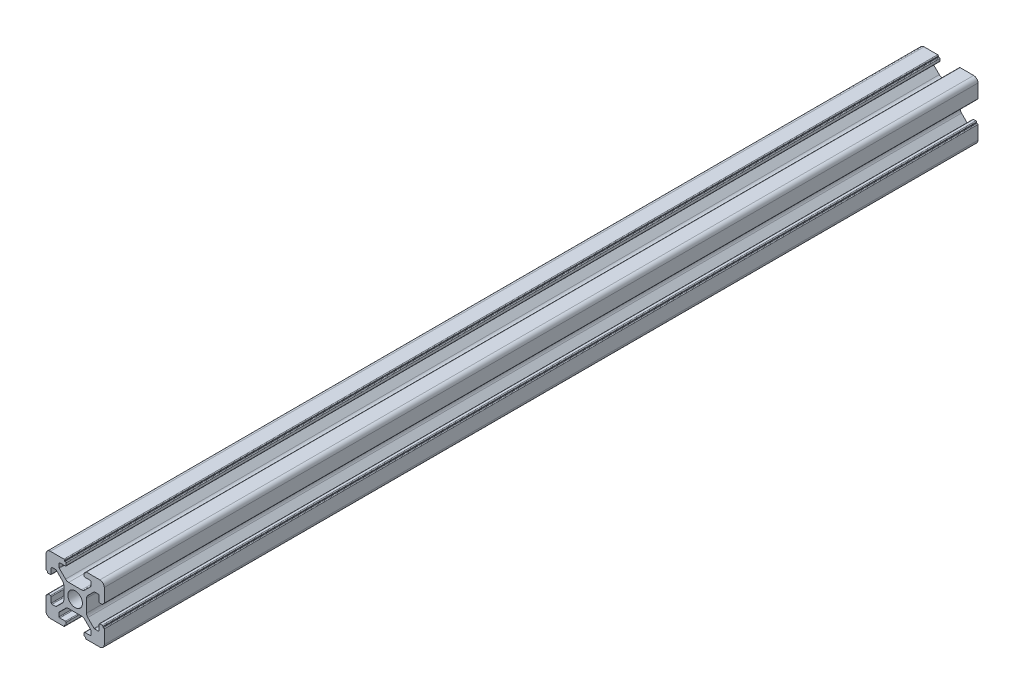
SolidWorks part; units mm, degrees
material "1060 Alloy"
ref_plane "前视基准面" through (0, 0, 0) normal (0, 0, 1) x (1, 0, 0)
ref_plane "上视基准面" through (0, 0, 0) normal (0, 1, 0) x (1, 0, 0)
ref_plane "右视基准面" through (0, 0, 0) normal (1, 0, 0) x (0, 0, -1)
sketch "草图1" plane through (0, 0, 0) normal (0, 0, 1) x (1, 0, 0)
  line L0 (0, 0) -> (0, 5.5) construction
  line L1 (-8.5023, -10.0023) -> (-3.85, -10.0023)
  line L2 (-10.0023, -8.5023) -> (-10.0023, -3.85)
  line L3 (-8.5023, 10.0023) -> (-3.85, 10.0023)
  line L4 (10.0023, -8.5023) -> (10.0023, -3.85)
  line L5 (-10.0023, -10.0023) -> (10.0023, 10.0023) construction
  line L6 (-10.0023, 10.0023) -> (10.0023, -10.0023) construction
  line L7 (-2.218, -3.9) -> (2.218, -3.9)
  line L8 (-3.9, -2.218) -> (-3.9, 2.218)
  line L9 (-2.218, 3.9) -> (2.218, 3.9)
  line L10 (3.9, -2.218) -> (3.9, 2.218)
  line L11 (-3.9, -3.9) -> (3.9, 3.9) construction
  line L12 (-3.9, 3.9) -> (3.9, -3.9) construction
  line L13 (-5.25, -8.2) -> (-3.35, -8.2)
  line L14 (-8.2, -5.25) -> (-8.2, -3.35)
  line L15 (-5.25, 8.2) -> (-3.35, 8.2)
  line L16 (8.2, -5.25) -> (8.2, -3.35)
  line L17 (-8.2, -8.2) -> (8.2, 8.2) construction
  line L18 (-8.2, 8.2) -> (8.2, -8.2) construction
  line L19 (-7.95, 5.5) -> (-6.6642, 5.5)
  line L20 (0, 0) -> (5.5, 0) construction
  line L23 (-5.5, 7.95) -> (-5.5, 6.6642)
  line L26 (0, 0) -> (-0.5303, 0.5303)
  line L27 (3.2787, 4.3393) -> (5.4268, 6.4874)
  line L28 (0, 0) -> (0.5303, -0.5303)
  line L29 (5.5, 6.6642) -> (5.5, 7.95)
  line L30 (4.3393, 3.2787) -> (6.4874, 5.4268)
  line L31 (6.6642, 5.5) -> (7.95, 5.5)
  line L32 (4.3393, -3.2787) -> (6.4874, -5.4268)
  line L33 (3.2787, -4.3393) -> (5.4268, -6.4874)
  line L34 (-3.2787, -4.3393) -> (-5.4268, -6.4874)
  line L35 (-4.3393, -3.2787) -> (-6.4874, -5.4268)
  line L36 (-4.3393, 3.2787) -> (-6.4874, 5.4268)
  line L37 (-3.2787, 4.3393) -> (-5.4268, 6.4874)
  line L38 (3.1, -8.45) -> (3.1, -9.2523)
  line L39 (8.45, 3.1) -> (9.2523, 3.1)
  line L40 (-5.5, -6.6642) -> (-5.5, -7.95)
  line L41 (-6.6642, -5.5) -> (-7.95, -5.5)
  line L42 (5.5, -6.6642) -> (5.5, -7.95)
  line L43 (6.6642, -5.5) -> (7.95, -5.5)
  line L44 (9.2523, -3.1) -> (8.45, -3.1)
  line L46 (10.0023, 3.85) -> (10.0023, 8.5023)
  line L47 (8.2, 3.35) -> (8.2, 5.25)
  line L48 (-3.1, -9.2523) -> (-3.1, -8.45)
  line L49 (-8.45, -3.1) -> (-9.2523, -3.1)
  line L50 (-9.2523, 3.1) -> (-8.45, 3.1)
  line L51 (-3.1, 8.45) -> (-3.1, 9.2523)
  line L52 (3.1, 9.2523) -> (3.1, 8.45)
  line L53 (3.85, 10.0023) -> (8.5023, 10.0023)
  line L54 (3.35, 8.2) -> (5.25, 8.2)
  line L55 (-10.0023, 3.85) -> (-10.0023, 8.5023)
  line L56 (-8.2, 3.35) -> (-8.2, 5.25)
  line L57 (3.35, -8.2) -> (5.25, -8.2)
  line L58 (3.85, -10.0023) -> (8.5023, -10.0023)
  line L59 (9.7523, -3.6) -> (9.5023, -3.6)
  line L61 (9.7523, 3.6) -> (9.5023, 3.6)
  line L62 (9.5023, -3.6) -> (9.5023, -3.35)
  line L63 (3.6, -9.7523) -> (3.6, -9.5023)
  line L64 (3.35, -9.5023) -> (3.6, -9.5023)
  line L65 (9.5023, 3.35) -> (9.5023, 3.6)
  line L66 (-3.6, -9.5023) -> (-3.35, -9.5023)
  line L67 (-3.6, -9.7523) -> (-3.6, -9.5023)
  line L68 (-9.7523, -3.6) -> (-9.5023, -3.6)
  line L69 (-9.5023, -3.35) -> (-9.5023, -3.6)
  line L70 (-9.5023, 3.6) -> (-9.5023, 3.35)
  line L71 (-9.7523, 3.6) -> (-9.5023, 3.6)
  line L72 (-3.6, 9.7523) -> (-3.6, 9.5023)
  line L73 (-3.35, 9.5023) -> (-3.6, 9.5023)
  line L74 (3.6, 9.5023) -> (3.35, 9.5023)
  line L75 (3.6, 9.7523) -> (3.6, 9.5023)
  circle A0 centre (0, 0) radius 2.5
  arc A1 (10.0023, 8.5023) -> (8.5023, 10.0023) centre (8.5023, 8.5023) ccw
  arc A2 (8.5023, -10.0023) -> (10.0023, -8.5023) centre (8.5023, -8.5023) ccw
  arc A3 (-10.0023, -8.5023) -> (-8.5023, -10.0023) centre (-8.5023, -8.5023) ccw
  arc A4 (-10.0023, 8.5023) -> (-8.5023, 10.0023) centre (-8.5023, 8.5023) cw
  arc A5 (-9.5023, -3.35) -> (-9.2523, -3.1) centre (-9.2523, -3.35) cw
  arc A6 (-9.7523, -3.6) -> (-10.0023, -3.85) centre (-9.7523, -3.85) ccw
  arc A7 (-8.45, -3.1) -> (-8.2, -3.35) centre (-8.45, -3.35) cw
  arc A8 (-7.95, -5.5) -> (-8.2, -5.25) centre (-7.95, -5.25) cw
  arc A9 (-6.4874, -5.4268) -> (-6.6642, -5.5) centre (-6.6642, -5.25) cw
  arc A10 (-5.4268, -6.4874) -> (-5.5, -6.6642) centre (-5.25, -6.6642) ccw
  arc A11 (-5.5, -7.95) -> (-5.25, -8.2) centre (-5.25, -7.95) ccw
  arc A12 (-3.6, -9.7523) -> (-3.85, -10.0023) centre (-3.85, -9.7523) cw
  arc A13 (-3.35, -9.5023) -> (-3.1, -9.2523) centre (-3.35, -9.2523) ccw
  arc A14 (-3.1, -8.45) -> (-3.35, -8.2) centre (-3.35, -8.45) ccw
  arc A15 (3.1, -8.45) -> (3.35, -8.2) centre (3.35, -8.45) cw
  arc A16 (5.5, -7.95) -> (5.25, -8.2) centre (5.25, -7.95) cw
  arc A17 (5.4268, -6.4874) -> (5.5, -6.6642) centre (5.25, -6.6642) cw
  arc A18 (6.4874, -5.4268) -> (6.6642, -5.5) centre (6.6642, -5.25) ccw
  arc A19 (7.95, -5.5) -> (8.2, -5.25) centre (7.95, -5.25) ccw
  arc A20 (8.45, -3.1) -> (8.2, -3.35) centre (8.45, -3.35) ccw
  arc A21 (9.5023, -3.35) -> (9.2523, -3.1) centre (9.2523, -3.35) ccw
  arc A22 (9.7523, -3.6) -> (10.0023, -3.85) centre (9.7523, -3.85) cw
  arc A23 (3.35, -9.5023) -> (3.1, -9.2523) centre (3.35, -9.2523) cw
  arc A24 (3.6, -9.7523) -> (3.85, -10.0023) centre (3.85, -9.7523) ccw
  arc A25 (7.95, 5.5) -> (8.2, 5.25) centre (7.95, 5.25) cw
  arc A26 (8.2, 3.35) -> (8.45, 3.1) centre (8.45, 3.35) ccw
  arc A27 (9.5023, 3.35) -> (9.2523, 3.1) centre (9.2523, 3.35) cw
  arc A28 (9.7523, 3.6) -> (10.0023, 3.85) centre (9.7523, 3.85) ccw
  arc A29 (6.6642, 5.5) -> (6.4874, 5.4268) centre (6.6642, 5.25) ccw
  arc A30 (5.4268, 6.4874) -> (5.5, 6.6642) centre (5.25, 6.6642) ccw
  arc A31 (5.5, 7.95) -> (5.25, 8.2) centre (5.25, 7.95) ccw
  arc A32 (3.1, 8.45) -> (3.35, 8.2) centre (3.35, 8.45) ccw
  arc A33 (3.6, 9.7523) -> (3.85, 10.0023) centre (3.85, 9.7523) cw
  arc A34 (3.35, 9.5023) -> (3.1, 9.2523) centre (3.35, 9.2523) ccw
  arc A35 (-9.7523, 3.6) -> (-10.0023, 3.85) centre (-9.7523, 3.85) cw
  arc A36 (-9.5023, 3.35) -> (-9.2523, 3.1) centre (-9.2523, 3.35) ccw
  arc A37 (-8.45, 3.1) -> (-8.2, 3.35) centre (-8.45, 3.35) ccw
  arc A38 (-8.2, 5.25) -> (-7.95, 5.5) centre (-7.95, 5.25) cw
  arc A39 (-6.4874, 5.4268) -> (-6.6642, 5.5) centre (-6.6642, 5.25) ccw
  arc A40 (-5.4268, 6.4874) -> (-5.5, 6.6642) centre (-5.25, 6.6642) cw
  arc A41 (-5.5, 7.95) -> (-5.25, 8.2) centre (-5.25, 7.95) cw
  arc A42 (-3.1, 8.45) -> (-3.35, 8.2) centre (-3.35, 8.45) cw
  arc A43 (-3.1, 9.2523) -> (-3.35, 9.5023) centre (-3.35, 9.2523) ccw
  arc A44 (-3.6, 9.7523) -> (-3.85, 10.0023) centre (-3.85, 9.7523) ccw
  arc A45 (-4.3393, 3.2787) -> (-3.9, 2.218) centre (-5.4, 2.218) cw
  arc A46 (-3.2787, 4.3393) -> (-2.218, 3.9) centre (-2.218, 5.4) ccw
  arc A47 (3.2787, 4.3393) -> (2.218, 3.9) centre (2.218, 5.4) cw
  arc A48 (4.3393, 3.2787) -> (3.9, 2.218) centre (5.4, 2.218) ccw
  arc A49 (4.3393, -3.2787) -> (3.9, -2.218) centre (5.4, -2.218) cw
  arc A50 (3.2787, -4.3393) -> (2.218, -3.9) centre (2.218, -5.4) ccw
  arc A51 (-4.3393, -3.2787) -> (-3.9, -2.218) centre (-5.4, -2.218) ccw
  arc A52 (-2.218, -3.9) -> (-3.2787, -4.3393) centre (-2.218, -5.4) ccw
  point P0 (0, 0)
  point P7 (10.0023, 0)
  point P62 (0, 0)
  point P76 (0, 0)
  point P92 (-8.2, -5.5)
  point P99 (0, 0)
  point P106 (-5.5, -8.2)
  point P117 (5.5, -8.2)
  point P124 (8.2, -5.5)
  point P137 (8.2, 5.5)
  point P140 (8.2, 3.1)
  point P147 (6.5607, 5.5)
  point P152 (5.5, 8.2)
  point P167 (-8.2, 5.5)
  point P174 (-5.5, 8.2)
  dimension "D1" = 1.5
  dimension "D5" = 0.25
  dimension "D6" = 1.5
  dimension "D2" = 4
  dimension "D3" = 4
  dimension "D4" = 4
extrude "凸台-拉伸1" add sketch "草图1" along normal blind 300 contours A52 L7 A50 L33 A17 L42 A16 L57 A15 L38 A23 L64 L63 A24 L58 A2 L4 A22 L59 L62 A21 L44 A20 L16 A19 L43 A18 L32 A49 L10 A48 L30 A29 L31 A25 L47 A26 L39 A27 L65 L61 A28 L46 A1 L53 A33 L75 L74 A34 L52 A32
ref_plane "Plane1" through (0, 0, 150) normal (0, 0, 1) x (1, 0, 0)
